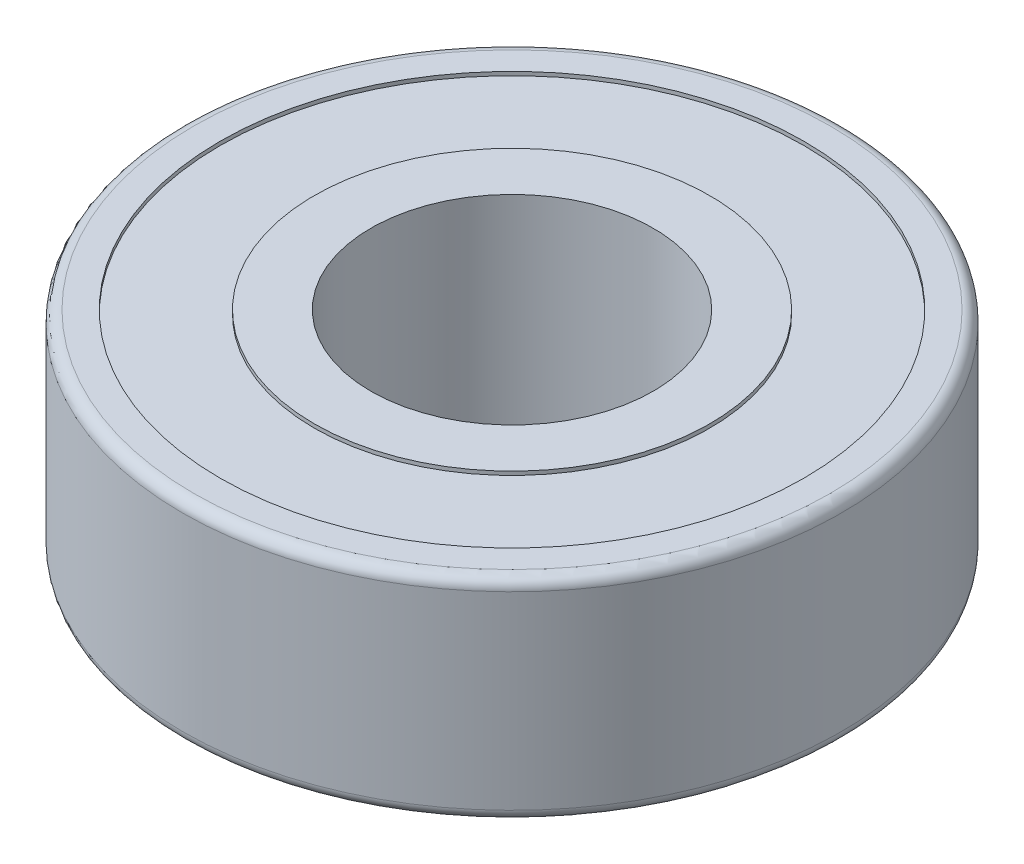
SolidWorks part; units mm, degrees
ref_plane "Front Plane" through (0, 0, 0) normal (0, 0, 1) x (1, 0, 0)
ref_plane "Top Plane" through (0, 0, 0) normal (0, 1, 0) x (1, 0, 0)
ref_plane "Right Plane" through (0, 0, 0) normal (1, 0, 0) x (0, 0, -1)
sketch "Sketch1" plane through (0, 0, 0) normal (0, 1, 0) x (1, 0, 0)
  circle A0 centre (0, 0) radius 11.1125
  circle A1 centre (0, 0) radius 4.7625
  dimension "D1" = 9.525
  dimension "D2" = 22.225
extrude "Boss-Extrude1" add sketch "Sketch1" along normal blind 7.1437
sketch "Sketch2" plane through (0, 7.1437, 0) normal (0, 1, 0) x (1, 0, 0)
  circle A0 centre (0, 0) radius 6.6675
  circle A1 centre (0, 0) radius 9.8425
  dimension "D1" = 13.335
  dimension "D2" = 19.685
extrude "Cut-Extrude1" cut sketch "Sketch2" against normal blind 0.127
sketch "Sketch3" plane through (0, 0, 0) normal (0, -1, 0) x (1, 0, 0)
  circle A0 centre (0, 0) radius 6.6675 construction
  circle A1 centre (0, 0) radius 9.8425 construction
  circle A2 centre (0, 0) radius 6.6675
  circle A3 centre (0, 0) radius 9.8425
extrude "Cut-Extrude3" cut sketch "Sketch3" against normal blind 0.127
fillet "Fillet1" radius 0.381 2 edges at (0, 0, 11.1125) (0, 7.1437, 11.1125)
